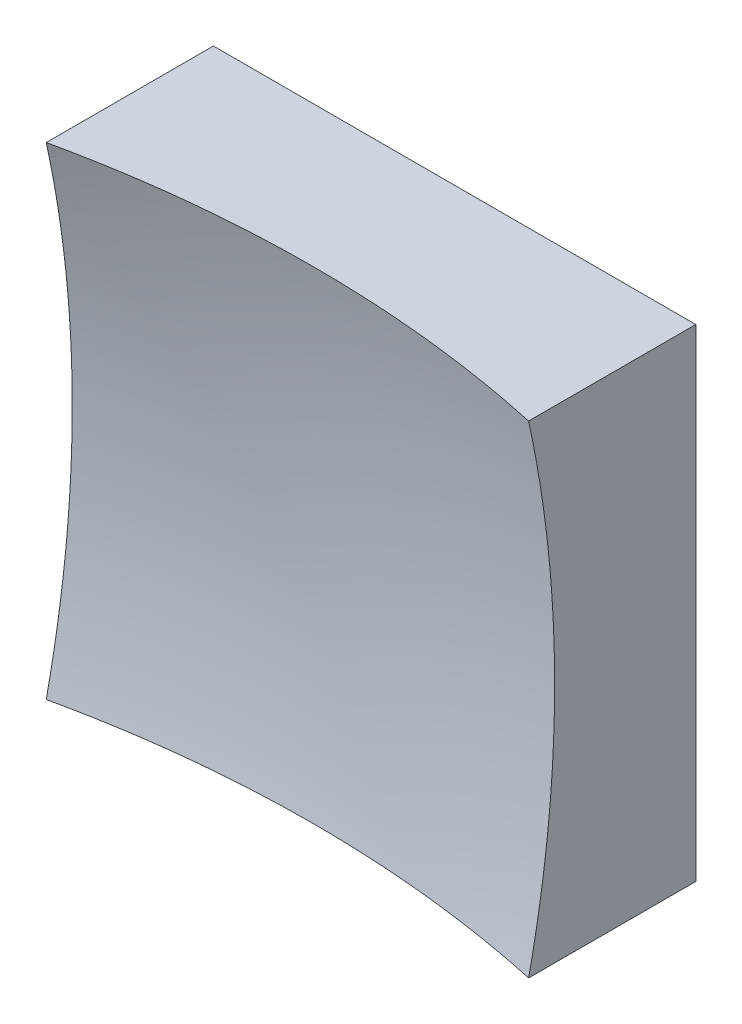
SolidWorks part; units mm, degrees
ref_plane "前视基准面" through (0, 0, 0) normal (0, 0, 1) x (1, 0, 0)
ref_plane "上视基准面" through (0, 0, 0) normal (0, 1, 0) x (1, 0, 0)
ref_plane "右视基准面" through (0, 0, 0) normal (1, 0, 0) x (0, 0, -1)
sketch "草图1" plane through (0, 0, 0) normal (0, 0, 1) x (1, 0, 0)
  line L1 (-12.5, 12.5) -> (12.5, 12.5)
  line L2 (-12.5, 12.5) -> (-12.5, -12.5)
  line L3 (-12.5, -12.5) -> (12.5, -12.5)
  line L4 (12.5, 12.5) -> (12.5, -12.5)
  line L5 (-12.5, 12.5) -> (12.5, -12.5) construction
  line L6 (-12.5, -12.5) -> (12.5, 12.5) construction
  point P0 (0, 0)
  dimension "D1" = 25
  dimension "D2" = 25
extrude "凸台-拉伸1" add sketch "草图1" along normal blind 20 contours L2 L3 L4 L1
sketch "草图2" plane through (0, 0, 0) normal (0, 1, 0) x (1, 0, 0)
  line L0 (-7.4603, -6) -> (7.3192, -6) construction
  line L1 (0, 0) -> (0, -12.1749) construction
  line L2 (58.4907, -52.6271) -> (0, -52.6271)
  line L3 (0, -52.6271) -> (0, -6)
  arc A1 (58.4907, -52.6271) -> (0, -6) centre (0, -66) ccw
  dimension "D2" = 120
  dimension "D1" = 6
revolve "切除-旋转2" cut sketch "草图2" angle 360 about L3
